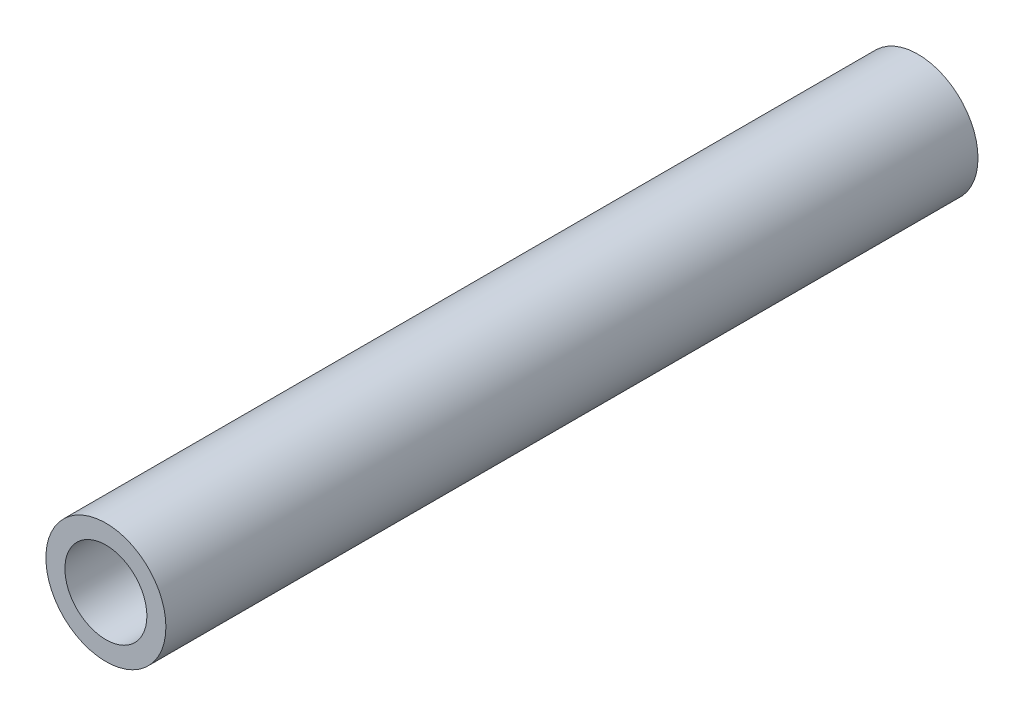
SolidWorks part; units mm, degrees
ref_plane "Plan de face" through (0, 0, 0) normal (0, 0, 1) x (1, 0, 0)
ref_plane "Plan de dessus" through (0, 0, 0) normal (0, 1, 0) x (1, 0, 0)
ref_plane "Plan de droite" through (0, 0, 0) normal (1, 0, 0) x (0, 0, -1)
sketch "Esquisse1" plane through (0, 0, 0) normal (0, 0, 1) x (1, 0, 0)
  circle A0 centre (0, 0) radius 4.1
  circle A1 centre (0, 0) radius 6
  dimension "D1" = 8.2
  dimension "D2" = 12
extrude "Boss.-Extru.1" add sketch "Esquisse1" along normal blind 81.2
